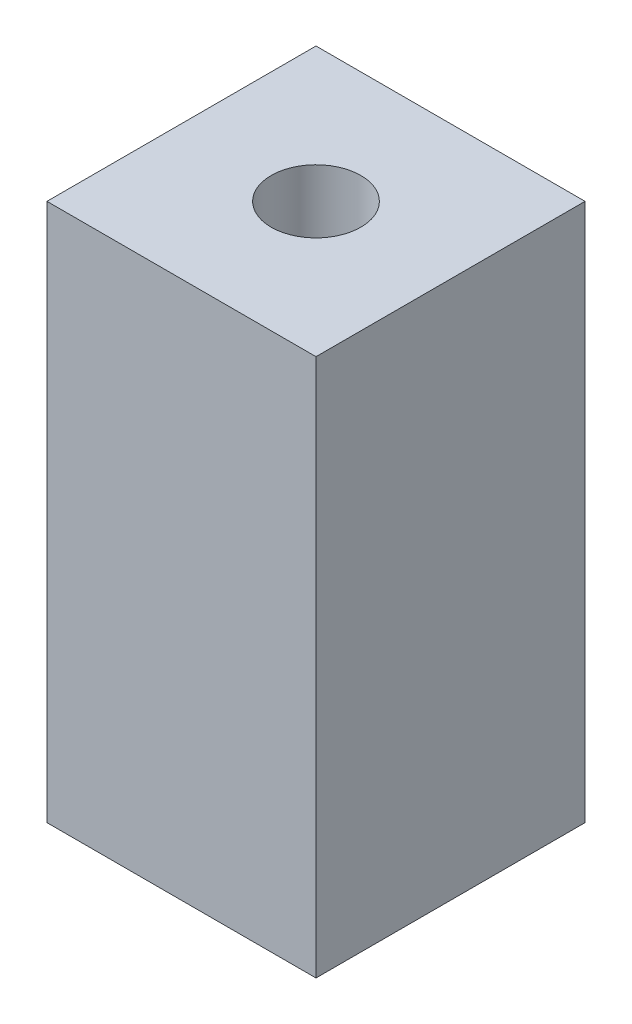
SolidWorks part; units mm, degrees
ref_plane "Front Plane" through (0, 0, 0) normal (0, 0, 1) x (1, 0, 0)
ref_plane "Top Plane" through (0, 0, 0) normal (0, 1, 0) x (1, 0, 0)
ref_plane "Right Plane" through (0, 0, 0) normal (1, 0, 0) x (0, 0, -1)
sketch "Sketch1" plane through (0, 0, 0) normal (0, 1, 0) x (1, 0, 0)
  line L1 (9.525, -9.525) -> (-9.525, -9.525)
  line L2 (9.525, -9.525) -> (9.525, 9.525)
  line L3 (9.525, 9.525) -> (-9.525, 9.525)
  line L4 (-9.525, -9.525) -> (-9.525, 9.525)
  line L5 (9.525, -9.525) -> (-9.525, 9.525) construction
  line L6 (9.525, 9.525) -> (-9.525, -9.525) construction
  circle A0 centre (0, 0) radius 3.175
  point P0 (0, 0)
  dimension "D1" = 6.35
  dimension "D2" = 19.05
  dimension "D3" = 19.05
extrude "Boss-Extrude1" add sketch "Sketch1" along normal blind 38.1
